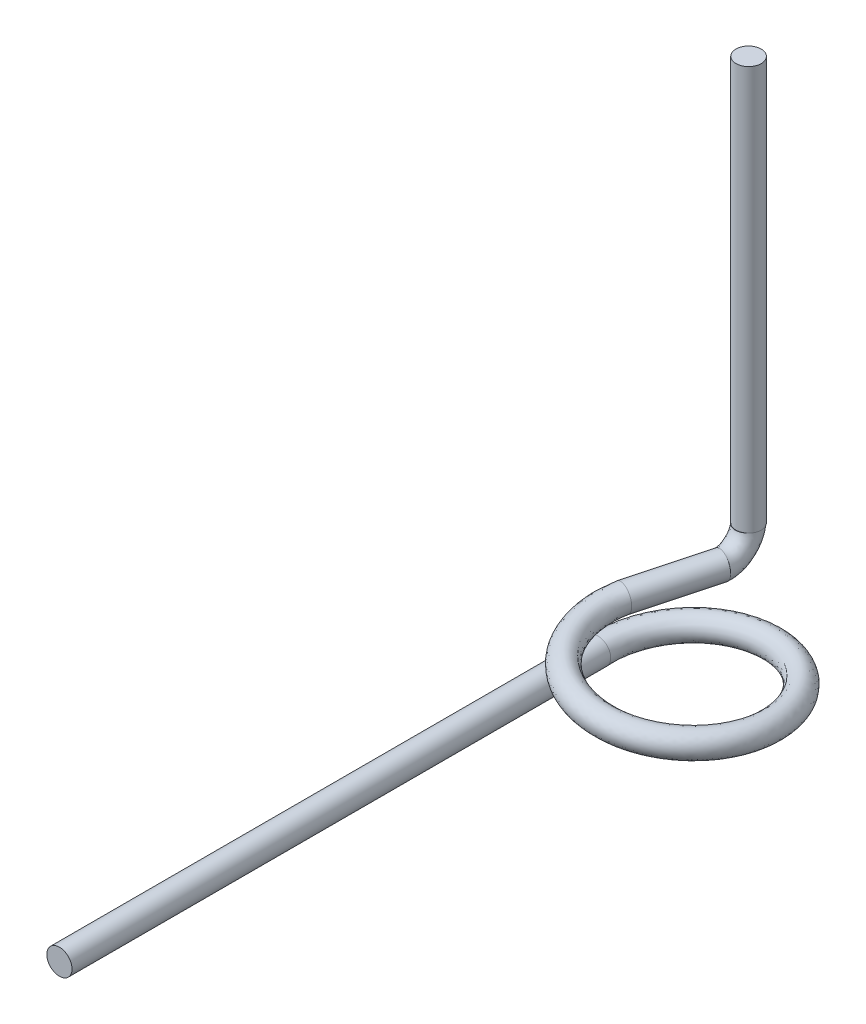
SolidWorks part; units mm, degrees
ref_plane "Front Plane" through (0, 0, 0) normal (0, 0, 1) x (1, 0, 0)
ref_plane "Top Plane" through (0, 0, 0) normal (0, 1, 0) x (1, 0, 0)
ref_plane "Right Plane" through (0, 0, 0) normal (1, 0, 0) x (0, 0, -1)
sketch "Sketch1" plane through (0, 0, 0) normal (0, 1, 0) x (1, 0, 0)
  circle A0 centre (0, 0) radius 15.875
  dimension "D1" = 31.75
curve "Helix/Spiral1" pitch 6.604 height 6.8792 turns 1.0417
ref_plane "Plane1" through (0, 0, 0) normal (0, 0, 1) x (1, 0, 0)
sketch "Sketch4" plane through (0, 0, 0) normal (0, 0, 1) x (1, 0, 0)
  circle A0 centre (-15.875, 0) radius 2.3813
  dimension "D1" = 4.7625
  dimension "D2" = 15.875
  dimension "D3" = 0
sweep "Sweep1" add profiles "Sketch4" path "Helix/Spiral1"
sketch "Sketch5" plane through (0, 0, 0) normal (0.2588, 0, -0.9659) x (-0.9659, 0, -0.2588)
  circle A0 centre (15.875, 6.8795) radius 2.3812
  circle A1 centre (15.875, 6.8795) radius 2.3812 construction
extrude "Boss-Extrude1" add sketch "Sketch5" along normal blind 15.24
sketch "Sketch6" plane through (0, 0, 0) normal (0, 0, 1) x (1, 0, 0)
  circle A0 centre (-15.875, 0) radius 2.3813
  circle A1 centre (-15.875, 0) radius 2.3813 construction
extrude "Boss-Extrude2" add sketch "Sketch6" along normal blind 101.6
sketch "Sketch7" plane through (3.9444, 0, -14.7207) normal (0.2588, 0, -0.9659) x (-0.9659, 0, -0.2588)
  circle A0 centre (15.875, 6.8795) radius 2.3813
  circle A1 centre (15.875, 6.8795) radius 2.3813 construction
  point P4 (0, 0)
  point P5 (0, 0)
ref_plane "Plane2" through (0, 6.8795, 0) normal (0, 1, 0) x (1, 0, 0)
ref_plane "Plane3" through (-11.3897, 0, 0) normal (1, 0, 0) x (0, 0, -1)
sketch "Sketch8" plane through (-11.3897, -1.8806, 0) normal (1, 0, 0) x (0, -1, 0)
  line L0 (-8.7601, 18.8295) -> (-18.9201, 18.8295) construction
  line L1 (-13.8401, 23.9095) -> (-13.8401, 13.7495) construction
  line L3 (-8.7601, 18.8295) -> (-8.7601, 4.1088) construction
  arc A1 (-8.7601, 18.8295) -> (-13.8401, 23.9095) centre (-13.8401, 18.8295) ccw
  dimension "D1" = 10.16
sweep "Sweep3" add profiles "Sketch7" path "Sketch8"
sketch "Sketch10" plane through (2.2269, 8.3109, 0) normal (0.2588, 0.9659, 0) x (0.9659, -0.2588, 0)
  circle A0 centre (-14.0969, 23.9095) radius 2.3813
  circle A1 centre (-14.0969, 23.9095) radius 2.3813 construction
ref_plane "Plane4" through (0, 11.1975, 0) normal (0, 1, 0) x (1, 0, 0)
sketch "Sketch11" plane through (0, 11.1975, 0) normal (0, 1, 0) x (1, 0, 0)
  line L0 (4.4953, 29.534) -> (4.4953, -0.4678) construction
sketch "Sketch13" plane through (0, 0, 0) normal (1, 0, 0) x (0, 0, -1)
  line L0 (29.534, 11.1975) -> (-0.4678, 11.1975) construction
  line L1 (-1.6091, 11.1975) -> (33.1145, 11.1975)
  line L2 (-1.6091, 11.1975) -> (-1.6091, 45.9211)
  line L3 (-1.6091, 45.9211) -> (33.1145, 45.9211)
  line L4 (33.1145, 11.1975) -> (33.1145, 45.9211)
  line L5 (-1.6091, 11.1975) -> (33.1145, 45.9211) construction
  line L6 (-1.6091, 45.9211) -> (33.1145, 11.1975) construction
  point P0 (15.7527, 28.5593)
  point P7 (10.3924, 28.5593)
  point P11 (-48.9932, 24.4055)
  dimension "D1" = 34.7236
extrude "Cut-Extrude1" cut sketch "Sketch13" against normal blind 76.2
sketch "Sketch15" plane through (0, 11.1975, 0) normal (0, 1, 0) x (1, 0, 0)
  circle A1 centre (-11.3721, 23.8739) radius 2.3813
  point P2 (-11.0067, 23.6555)
  point P3 (-11.3474, 23.979)
  point P4 (0, 0)
  point P5 (-11.3721, 23.8739)
  dimension "D1" = 4.7625
extrude "Boss-Extrude5" add sketch "Sketch15" along normal blind 76.2
